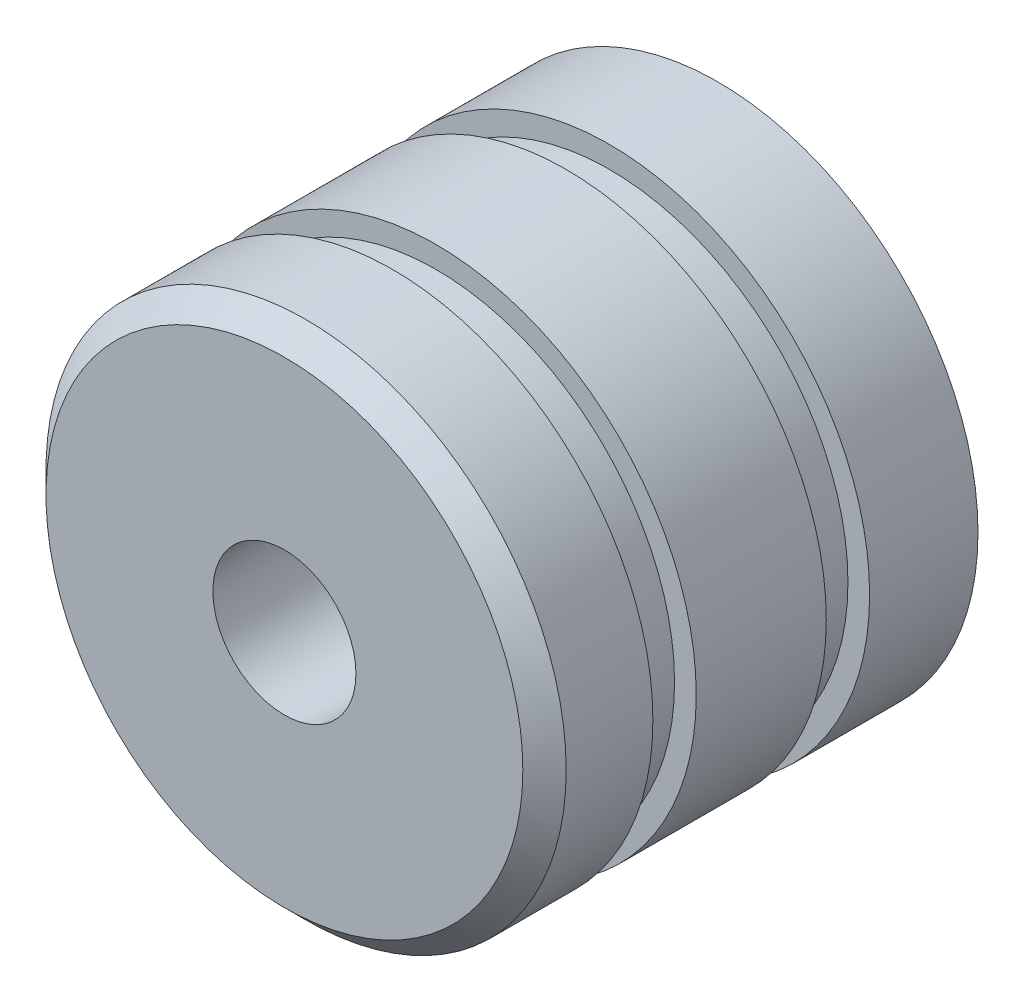
SolidWorks part; units mm, degrees
ref_plane "Front Plane" through (0, 0, 0) normal (0, 0, 1) x (1, 0, 0)
ref_plane "Top Plane" through (0, 0, 0) normal (0, 1, 0) x (1, 0, 0)
ref_plane "Right Plane" through (0, 0, 0) normal (1, 0, 0) x (0, 0, -1)
sketch "Sketch1" plane through (0, 0, 0) normal (0, 0, 1) x (1, 0, 0)
  circle A0 centre (0, 0) radius 6
  dimension "D1" = 12
extrude "Boss-Extrude1" add sketch "Sketch1" along normal mid plane 10
sketch "Sketch2" plane through (0, 0, 5) normal (0, 0, 1) x (1, 0, 0)
  circle A0 centre (0, 0) radius 5.5
  circle A1 centre (0, 0) radius 6 construction
  circle A2 centre (0, 0) radius 6
  dimension "D1" = 11
extrude "Cut-Extrude1" cut sketch "Sketch2" against normal blind 1 from offset 2.5 offset against normal yes
mirror "Mirror1" about plane through (0, 0, 0) normal (0, 0, 1) of "Cut-Extrude1"
chamfer "Chamfer1" distance 0.5 angle 45 1 edges at (6, 0, 5)
sketch "Sketch6" plane through (0, 0, 5) normal (0, 0, 1) x (1, 0, 0)
  point P0 (0, 0)
sketch "Sketch10" plane through (0, 0, 5) normal (0, 0, 1) x (1, 0, 0)
  point P0 (0, 0)
hole_wizard "M4x0.7 Tapped Hole1" positions "Sketch10" profile "Sketch9" tap size "M4x0.7" standard "ANSI Metric"
sketch "Sketch9" plane through (0, 0, 5) normal (1, 0, 0) x (0, -1, 0)
  line L0 (0, 0) -> (0, 8.9914)
  line L1 (0, 8.9914) -> (1.65, 8)
  line L2 (1.65, 8) -> (1.65, 0)
  line L5 (1.65, 0) -> (0, 0)
  line L10 (0, 8.9914) -> (-1.65, 8) construction
  line L11 (0, -6.35) -> (0, 107.95) construction
  dimension "Tap Drill Dia." = 3.3
  dimension "Tap Drill Depth" = 8
  dimension "Drill Angle" = 118
cosmetic thread "Hole Thread2"
